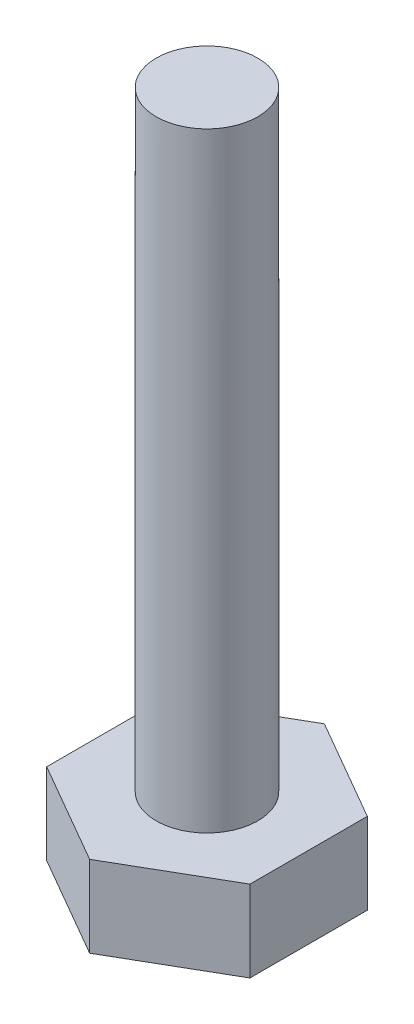
SolidWorks part; units mm, degrees
ref_plane "Front Plane" through (0, 0, 0) normal (0, 0, 1) x (1, 0, 0)
ref_plane "Top Plane" through (0, 0, 0) normal (0, 1, 0) x (1, 0, 0)
ref_plane "Right Plane" through (0, 0, 0) normal (1, 0, 0) x (0, 0, -1)
sketch "Sketch1" plane through (0, 0, 0) normal (0, 1, 0) x (1, 0, 0)
  circle A0 centre (0, 0) radius 2.5
extrude "Boss-Extrude1" add sketch "Sketch1" along normal blind 30
sketch "Sketch2" plane through (0, 0, 0) normal (0, -1, 0) x (1, 0, 0)
  line L1 (0, 5.7735) -> (-5, 2.8868)
  line L2 (-5, 2.8868) -> (-5, -2.8868)
  line L3 (-5, -2.8868) -> (0, -5.7735)
  line L4 (0, -5.7735) -> (5, -2.8868)
  line L5 (5, -2.8868) -> (5, 2.8868)
  line L6 (5, 2.8868) -> (0, 5.7735)
  circle A0 centre (0, 0) radius 5 construction
extrude "Boss-Extrude2" add sketch "Sketch2" along normal blind 4
